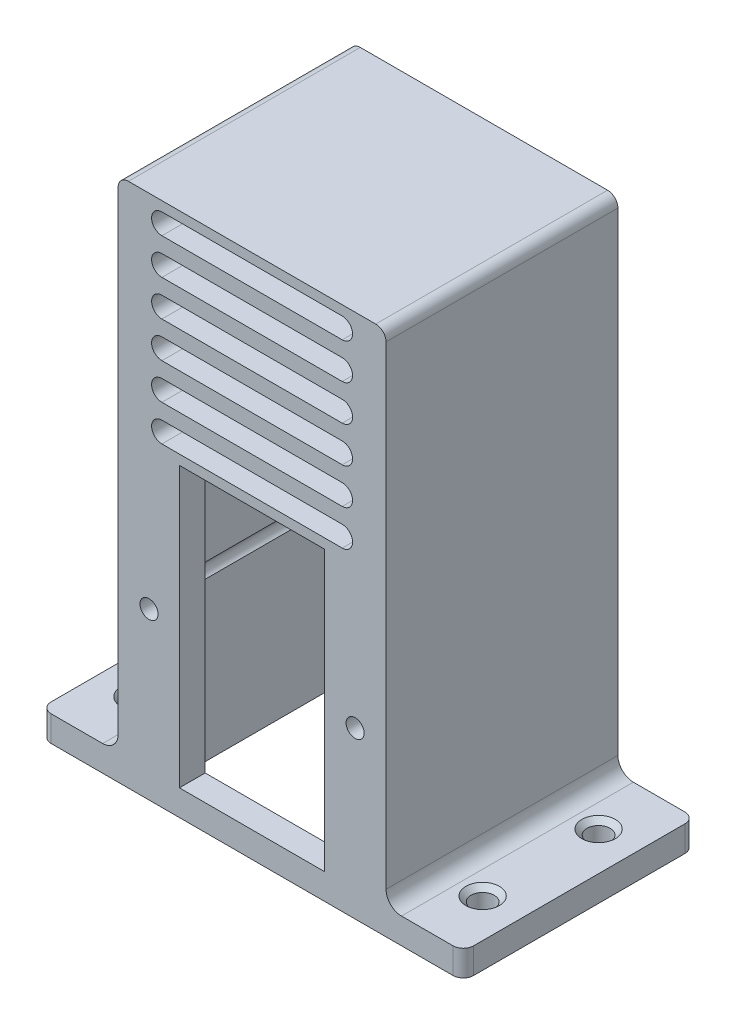
SolidWorks part; units mm, degrees
material "ABS"
ref_plane "Plano frontal" through (0, 0, 0) normal (0, 0, 1) x (1, 0, 0)
ref_plane "Plano superior" through (0, 0, 0) normal (0, 1, 0) x (1, 0, 0)
ref_plane "Plano direito" through (0, 0, 0) normal (1, 0, 0) x (0, 0, -1)
sketch "Esboço7" plane through (0, 0, 0) normal (0, 1, 0) x (1, 0, 0)
  line L0 (-21, 0) -> (21, 0)
  line L1 (21, 0) -> (26, 0)
  line L2 (-21, 0) -> (-26, 0)
  line L3 (26, 0) -> (41, 0)
  line L4 (-26, 0) -> (-41, 0)
  line L5 (-41, 0) -> (-41, 5)
  line L6 (-41, 5) -> (-41, 45)
  line L7 (41, 0) -> (41, 5)
  line L8 (41, 5) -> (41, 45)
  line L9 (-41, 45) -> (41, 45)
  line L10 (-41, 5) -> (41, 5) construction
  line L11 (-21, 5) -> (-21, 45)
  line L12 (-21, 5) -> (21, 5)
  line L13 (21, 5) -> (21, 45)
  line L14 (-26, 0) -> (-26, 45)
  line L15 (26, 0) -> (26, 45)
  point P4 (0, 0)
  dimension "D1" = 42
  dimension "D2" = 5
  dimension "D3" = 42
  dimension "D5" = 15
  dimension "D7" = 40
extrude "Ressalto-extrusão4" add sketch "Esboço7" along normal blind 5 contours L6 L10 L14 L9 | L14 L10 L11 L9 | L10 L5 L4 L14 | L10 L15 L3 L7 | L15 L10 L8 L9 | L13 L10 L15 L9 | L10 L14 L2 L0 L1 L15 L12
sketch "Esboço8" plane through (0, 0, 0) normal (0, 1, 0) x (1, 0, 0)
  line L0 (-21, 45) -> (-26, 45)
  line L1 (-41, 45) -> (-21, 45) construction
  line L2 (-26, 45) -> (-26, 0)
  line L3 (41, 0) -> (-41, 0) construction
  line L4 (-26, 0) -> (26, 0)
  line L5 (26, 0) -> (26, 45)
  line L6 (21, 45) -> (41, 45) construction
  line L7 (26, 45) -> (21, 45)
  line L8 (21, 5) -> (21, 45) construction
  line L9 (21, 45) -> (21, 5)
  line L10 (21, 5) -> (-21, 5)
  line L11 (-21, 5) -> (-21, 45)
  dimension "D1" = 5
extrude "Ressalto-extrusão6" add sketch "Esboço8" along normal blind 102
sketch "Esboço9" plane through (0, 0, 0) normal (0, 0, 1) x (1, 0, 0)
  line L0 (-26, 102) -> (-26, 97)
  line L1 (-26, 102) -> (-26, 5) construction
  line L2 (-26, 97) -> (26, 97)
  line L3 (26, 102) -> (26, 5) construction
  line L4 (26, 97) -> (26, 102)
  line L5 (-26, 102) -> (26, 102) construction
  line L6 (26, 102) -> (-26, 102)
  dimension "D1" = 5
extrude "Ressalto-extrusão7" add sketch "Esboço9" against normal blind 45
sketch "Esboço10" plane through (0, 0, 0) normal (0, 1, 0) x (1, 0, 0)
  line L0 (-41, 0) -> (-41, 45) construction
  line L1 (-41, 45) -> (-26, 45) construction
  line L2 (-41, 22.5) -> (41, 22.5) construction
  line L3 (41, 0) -> (41, 45) construction
  line L4 (0, 45) -> (0, 0) construction
  line L5 (26, 45) -> (-26, 45) construction
  circle A0 centre (-33.5, 33.75) radius 2.25
  circle A4 centre (-33.5, 11.25) radius 2.25
  circle A5 centre (33.5, 11.25) radius 2.25
  circle A6 centre (33.5, 33.75) radius 2.25
  dimension "D1" = 4.5
  dimension "D2" = 7.5
  dimension "D3" = 11.25
extrude "Corte-extrusão1" cut sketch "Esboço10" along normal through all
fillet "Filete1" radius 3 2 edges at (26, 5, -22.5) (-26, 5, -22.5)
fillet "Filete3" radius 2 4 edges at (41, 2.5, 0) (41, 2.5, -45) (-41, 2.5, 0) (-41, 2.5, -45)
fillet "Filete5" radius 2 2 edges at (26, 102, -22.5) (-26, 102, -22.5)
sketch "Esboço11" plane through (0, 0, 0) normal (0, 0, 1) x (1, 0, 0)
  line L0 (39, 0) -> (-39, 0) construction
  line L1 (-26, 100) -> (-26, 8) construction
  line L2 (0, 0) -> (0, 102) construction
  line L3 (-24, 102) -> (24, 102) construction
  line L4 (-14.1, 5) -> (14.1, 5)
  line L5 (14.1, 5) -> (14.1, 59.2)
  line L6 (14.1, 59.2) -> (-14.1, 59.2)
  line L7 (-14.1, 59.2) -> (-14.1, 5)
  circle A0 centre (20, 32.1) radius 1.75
  circle A2 centre (-20, 32.1) radius 1.75
  point P5 (0, 5)
  point P13 (0, 5)
  point P14 (14.1, 32.1)
  dimension "D6" = 3.5
  dimension "D4" = 5.9
  dimension "D1" = 5
  dimension "D2" = 28.2
  dimension "D3" = 54.2
  dimension "D5" = 32.1
  dimension "D7" = 11.9
extrude "Corte-extrusão2" cut sketch "Esboço11" against normal through all
sketch "Esboço12" plane through (0, 0, 0) normal (0, 0, 1) x (1, 0, 0)
  line L0 (0, 98.1) -> (17.5, 98.1) construction
  line L1 (0, 102) -> (0, 59.2) construction
  line L2 (-24, 102) -> (24, 102) construction
  line L3 (14.1, 59.2) -> (-14.1, 59.2) construction
  line L4 (-17.5, 98.1) -> (17.5, 98.1) construction
  line L5 (-17.5, 100.1) -> (17.5, 100.1)
  line L6 (-17.5, 96.1) -> (17.5, 96.1)
  line L7 (-17.5, 91.1) -> (17.5, 91.1) construction
  line L8 (-17.5, 93.1) -> (17.5, 93.1)
  line L9 (-17.5, 89.1) -> (17.5, 89.1)
  line L10 (-17.5, 84.1) -> (17.5, 84.1) construction
  line L11 (-17.5, 86.1) -> (17.5, 86.1)
  line L12 (-17.5, 82.1) -> (17.5, 82.1)
  line L13 (-17.5, 77.1) -> (17.5, 77.1) construction
  line L14 (-17.5, 79.1) -> (17.5, 79.1)
  line L15 (-17.5, 75.1) -> (17.5, 75.1)
  line L16 (-17.5, 70.1) -> (17.5, 70.1) construction
  line L17 (-17.5, 72.1) -> (17.5, 72.1)
  line L18 (-17.5, 68.1) -> (17.5, 68.1)
  line L19 (-17.5, 63.1) -> (17.5, 63.1) construction
  line L20 (-17.5, 65.1) -> (17.5, 65.1)
  line L21 (-17.5, 61.1) -> (17.5, 61.1)
  arc A0 (-17.5, 100.1) -> (-17.5, 96.1) centre (-17.5, 98.1) ccw
  arc A1 (17.5, 96.1) -> (17.5, 100.1) centre (17.5, 98.1) ccw
  arc A2 (-17.5, 93.1) -> (-17.5, 89.1) centre (-17.5, 91.1) ccw
  arc A3 (17.5, 89.1) -> (17.5, 93.1) centre (17.5, 91.1) ccw
  arc A4 (-17.5, 86.1) -> (-17.5, 82.1) centre (-17.5, 84.1) ccw
  arc A5 (17.5, 82.1) -> (17.5, 86.1) centre (17.5, 84.1) ccw
  arc A6 (-17.5, 79.1) -> (-17.5, 75.1) centre (-17.5, 77.1) ccw
  arc A7 (17.5, 75.1) -> (17.5, 79.1) centre (17.5, 77.1) ccw
  arc A8 (-17.5, 72.1) -> (-17.5, 68.1) centre (-17.5, 70.1) ccw
  arc A9 (17.5, 68.1) -> (17.5, 72.1) centre (17.5, 70.1) ccw
  arc A10 (-17.5, 65.1) -> (-17.5, 61.1) centre (-17.5, 63.1) ccw
  arc A11 (17.5, 61.1) -> (17.5, 65.1) centre (17.5, 63.1) ccw
  point P3 (0, 98.1)
  point P6 (0, 80.6)
  point P15 (0, 91.1)
  point P22 (0, 84.1)
  point P33 (0, 77.1)
  point P40 (0, 70.1)
  point P47 (0, 63.1)
  dimension "D1" = 3.9
  dimension "D4" = 6
  dimension "D3" = 2
  dimension "D2" = 35
  dimension "D5" = 3
extrude "Corte-extrusão3" cut sketch "Esboço12" against normal through all
chamfer "Chanfro1" distance 1 angle 45 4 edges at (-33.5, 5, -31.5) (33.5, 5, -31.5) (33.5, 5, -9) (-33.5, 5, -9)
